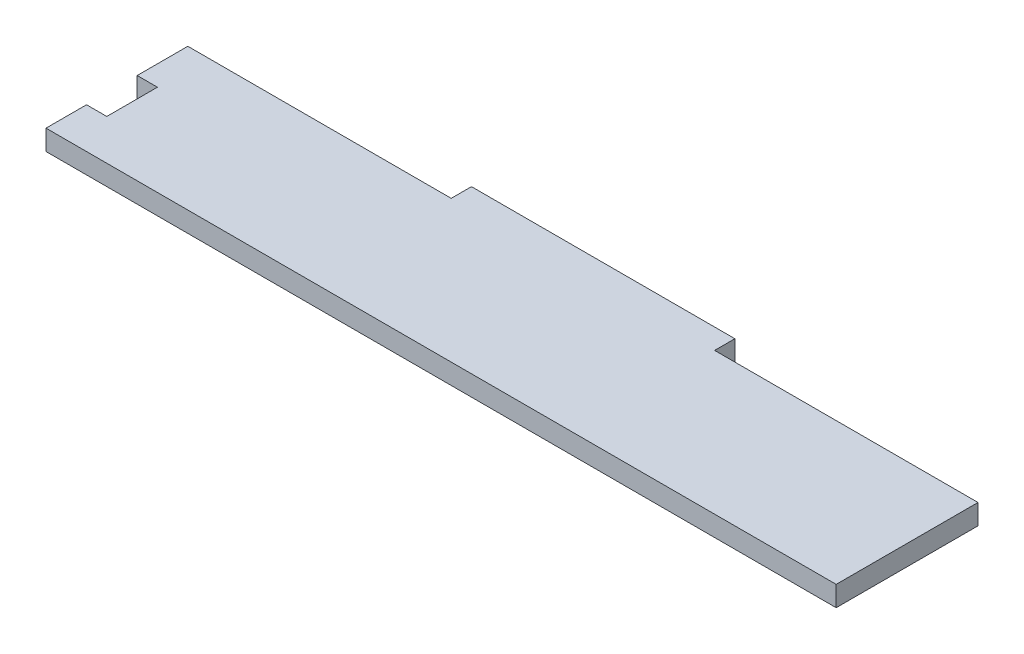
SolidWorks part; units mm, degrees
ref_plane "Front Plane" through (0, 0, 0) normal (0, 0, 1) x (1, 0, 0)
ref_plane "Top Plane" through (0, 0, 0) normal (0, 1, 0) x (1, 0, 0)
ref_plane "Right Plane" through (0, 0, 0) normal (1, 0, 0) x (0, 0, -1)
sketch "Sketch1" plane through (0, 0, 0) normal (0, 1, 0) x (1, 0, 0)
  line L36 (0, 70) -> (-390, 70)
  line L43 (0, 140) -> (0, 70)
  line L44 (0, 140) -> (-130, 140)
  line L45 (-130, 140) -> (-130, 150)
  line L46 (-130, 150) -> (-260, 150)
  line L47 (-260, 150) -> (-260, 140)
  line L48 (-260, 140) -> (-390, 140)
  line L49 (-390, 70) -> (-390, 90)
  line L50 (-390, 90) -> (-380, 90)
  line L51 (-380, 90) -> (-380, 115)
  line L52 (-380, 115) -> (-390, 115)
  line L53 (-390, 115) -> (-390, 140)
extrude "Boss-Extrude1" add sketch "Sketch1" along normal blind 10
